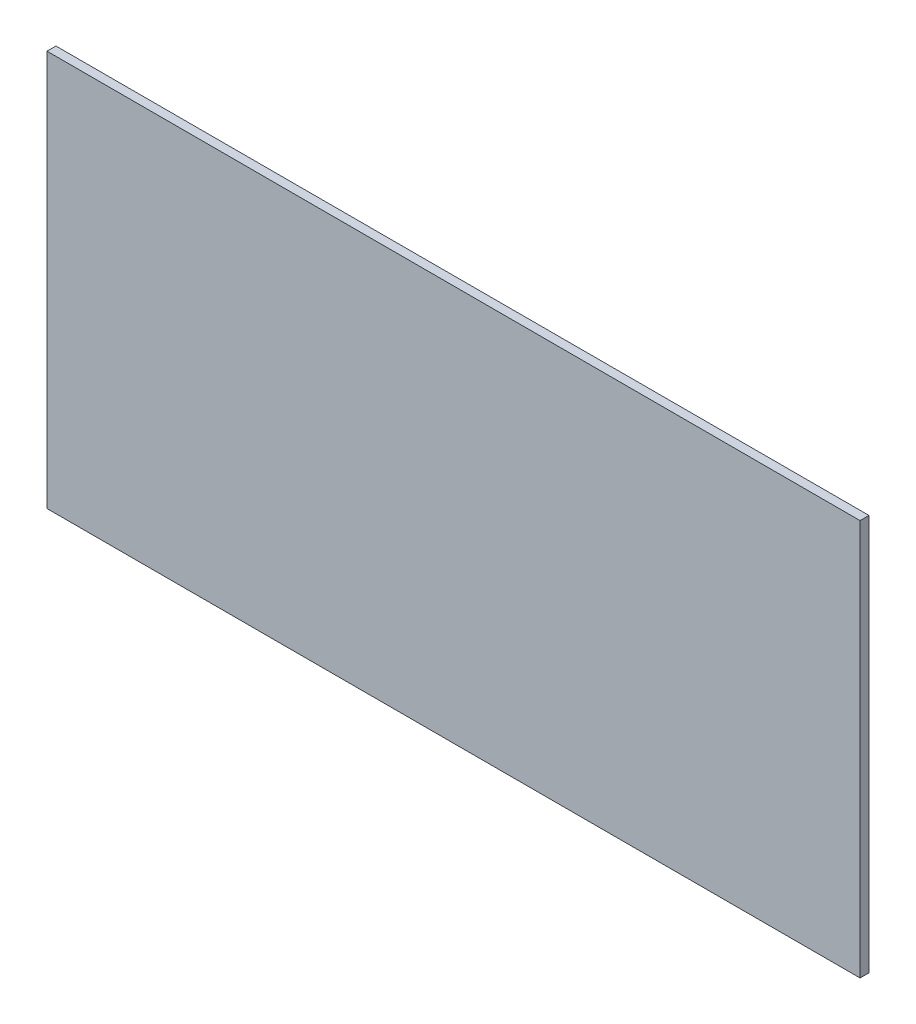
SolidWorks part; units mm, degrees
ref_plane "Plan de face" through (0, 0, 0) normal (0, 0, 1) x (1, 0, 0)
ref_plane "Plan de dessus" through (0, 0, 0) normal (0, 1, 0) x (1, 0, 0)
ref_plane "Plan de droite" through (0, 0, 0) normal (1, 0, 0) x (0, 0, -1)
sketch "Esquisse1" plane through (0, 0, 0) normal (0, 0, 1) x (1, 0, 0)
  line L1 (-38.0757, 29.0301) -> (234.9243, 29.0301)
  line L2 (-38.0757, 29.0301) -> (-38.0757, -103.9699)
  line L3 (-38.0757, -103.9699) -> (234.9243, -103.9699)
  line L4 (234.9243, 29.0301) -> (234.9243, -103.9699)
  dimension "D1" = 273
  dimension "D2" = 133
extrude "Boss.-Extru.1" add sketch "Esquisse1" along normal blind 3
equation "\"LongueurSyphon\"=270"
equation "\"D1@Esquisse1\" = \"LongueurSyphon\" + \"EpaisseurPlaque\""
equation "\"ProfondeurBoite\"=460"
equation "\"LargeurSyphon\"=120"
equation "\"EpaisseurPlaque\"= 3"
equation "\"HauteurSyphon\"=\"HauteurCoteGauche\"-\"HauteurSolSyphon\""
equation "\"D2@Esquisse1\"=\"LargeurBoite\" - \"LargeurGauche\" + \"EpaisseurPlaque\""
equation "\"HauteurCoteDroit\"= 490"
equation "\"HauteurCoteGauche\"= 540"
equation "\"HauteurSolSyphon\"= 300"
equation "\"LargeurDroite\"=10"
equation "\"LargeurGauche\"=150"
equation "\"LargeurBoite\"= \"LargeurDroite\" + \"LargeurGauche\" + \"LargeurSyphon\""
